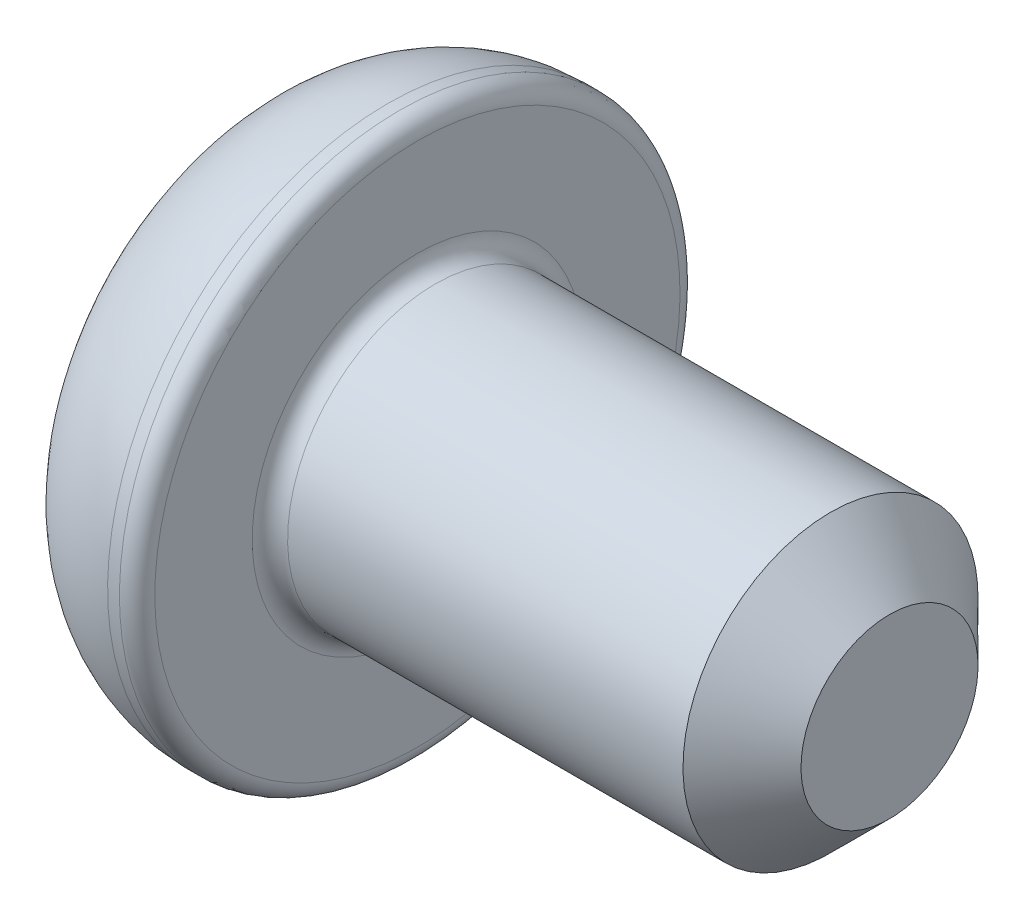
SolidWorks part; units mm, degrees
ref_plane "Спереди" through (0, 0, 0) normal (0, 0, 1) x (1, 0, 0)
ref_plane "Сверху" through (0, 0, 0) normal (0, 1, 0) x (1, 0, 0)
ref_plane "Справа" through (0, 0, 0) normal (1, 0, 0) x (0, 0, -1)
sketch "Эскиз1" plane through (0, 0, 0) normal (0, 0, 1) x (1, 0, 0)
  line L0 (0, 0) -> (0, 3.625)
  line L1 (2.1, 4.75) -> (2.6, 4.75)
  line L2 (2.6, 4.75) -> (2.6, 2.5)
  line L3 (2.6, 2.5) -> (10.6, 2.5)
  line L4 (10.6, 2.5) -> (10.6, 0)
  line L5 (10.6, 0) -> (0, 0) construction
  line L6 (0, 0) -> (10.6, 0)
  arc A0 (0, 3.625) -> (2.1, 4.75) centre (2.1, 2.2275) cw
  point P9 (2.6, 3.625)
  dimension "D1" = 0.5
  dimension "D2" = 5
  dimension "D3" = 9.5
  dimension "D5" = 2.6
  dimension "D6" = 8
revolve "Повернуть1" add sketch "Эскиз1" angle 360 about L5
cosmetic thread "Условное изображение резьбы1" parameters "D2"=4.11
sketch "Эскиз2" plane through (0, 0, 0) normal (-1, 0, 0) x (0, 0, 1)
  line L1 (0.866, 1.5) -> (-0.866, 1.5)
  line L2 (-0.866, 1.5) -> (-1.7321, 0)
  line L3 (-1.7321, 0) -> (-0.866, -1.5)
  line L4 (-0.866, -1.5) -> (0.866, -1.5)
  line L5 (0.866, -1.5) -> (1.7321, 0)
  line L6 (1.7321, 0) -> (0.866, 1.5)
  circle A0 centre (0, 0) radius 1.5 construction
  dimension "D1" = 3
extrude "Вырез-Вытянуть1" cut sketch "Эскиз2" against normal blind 1.5
fillet "Скругление1" radius 0.3 2 edges at (2.6, 2.5, 0) (2.6, 4.75, 0)
chamfer "Фаска1" distance 1 angle 45 1 edges at (10.6, 2.5, 0)
